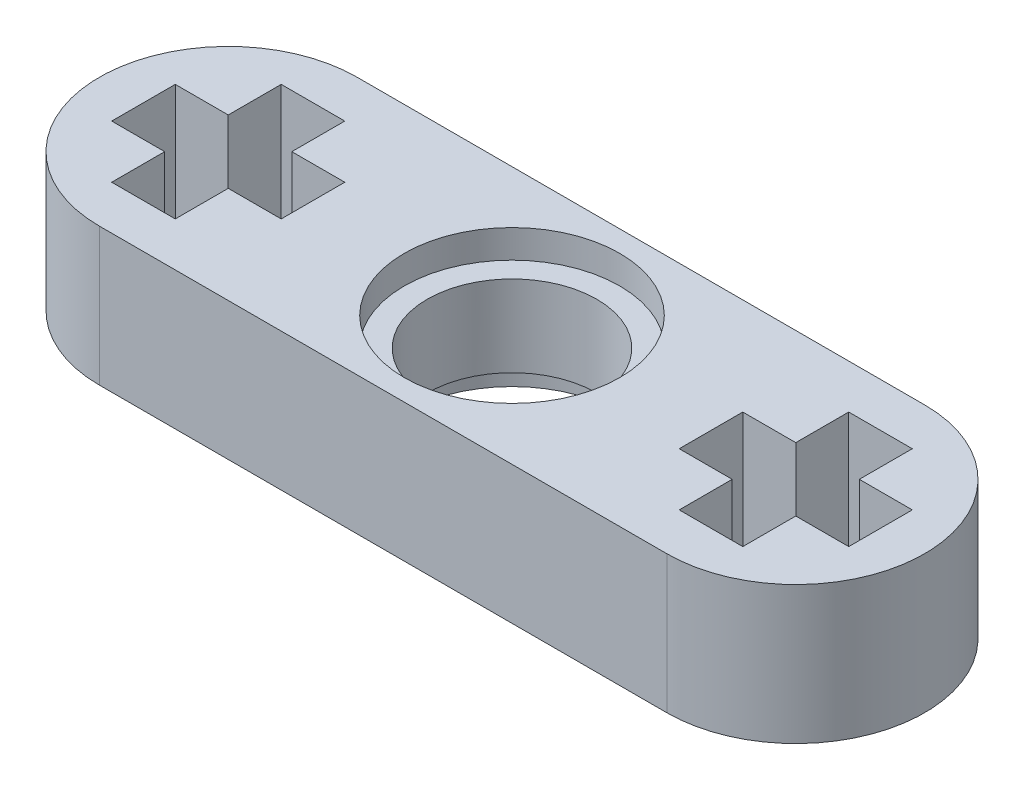
SolidWorks part; units mm, degrees
ref_plane "Front Plane" through (0, 0, 0) normal (0, 0, 1) x (1, 0, 0)
ref_plane "Top Plane" through (0, 0, 0) normal (0, 1, 0) x (1, 0, 0)
ref_plane "Right Plane" through (0, 0, 0) normal (1, 0, 0) x (0, 0, -1)
sketch "Sketch1" plane through (0, 0, 0) normal (0, 1, 0) x (1, 0, 0)
  line L0 (-8.035, 0) -> (-8.0349, 0) construction
  line L1 (-55, 0) -> (55, 0) construction
  line L2 (-8.035, 3.65) -> (8.035, 3.65)
  line L3 (-8.035, -3.65) -> (8.035, -3.65)
  line L4 (-11.685, 0) -> (-11.685, -5.5699) construction
  line L5 (-10.435, 0) -> (-10.435, -5.5699) construction
  line L6 (7.135, 2.4) -> (7.135, 0.9)
  line L7 (7.135, 2.4) -> (8.935, 2.4)
  line L8 (7.135, -2.4) -> (8.935, -2.4)
  line L9 (8.935, 2.4) -> (8.935, 0.9)
  line L10 (7.135, 2.4) -> (8.935, -2.4) construction
  line L11 (7.135, -2.4) -> (8.935, 2.4) construction
  line L12 (10.435, -0.9) -> (8.935, -0.9)
  line L13 (10.435, -0.9) -> (10.435, 0.9)
  line L14 (5.635, -0.9) -> (5.635, 0.9)
  line L15 (10.435, 0.9) -> (8.935, 0.9)
  line L16 (10.435, -0.9) -> (5.635, 0.9) construction
  line L17 (5.635, -0.9) -> (10.435, 0.9) construction
  line L18 (7.135, 0.9) -> (5.635, 0.9)
  line L19 (7.135, -0.9) -> (5.635, -0.9)
  line L20 (7.135, -0.9) -> (7.135, -2.4)
  line L21 (8.935, -0.9) -> (8.935, -2.4)
  line L34 (-8.935, 2.4001) -> (-8.935, 0.9001)
  line L35 (-8.935, 2.4001) -> (-7.135, 2.4001)
  line L36 (-8.935, -2.3999) -> (-7.135, -2.3999)
  line L37 (-7.135, 2.4001) -> (-7.135, 0.9001)
  line L38 (-5.635, -0.8999) -> (-7.135, -0.8999)
  line L39 (-5.635, -0.8999) -> (-5.635, 0.9001)
  line L40 (-10.435, -0.8999) -> (-10.435, 0.9001)
  line L41 (-5.635, 0.9001) -> (-7.135, 0.9001)
  line L42 (-8.935, 0.9001) -> (-10.435, 0.9001)
  line L43 (-8.935, -0.8999) -> (-10.435, -0.8999)
  line L44 (-8.935, -0.8999) -> (-8.935, -2.3999)
  line L45 (-7.135, -0.8999) -> (-7.135, -2.3999)
  line L46 (-8.935, 0.9001) -> (-7.135, -0.8999) construction
  line L47 (-8.035, 0.0001) -> (-7.135, 0.9001) construction
  line L48 (-5.635, 0) -> (8.035, 0) construction
  arc A0 (-8.035, 3.65) -> (-8.035, -3.65) centre (-8.035, 0) ccw
  arc A1 (8.035, -3.65) -> (8.035, 3.65) centre (8.035, 0) ccw
  circle A2 centre (0, 0) radius 2.4
  point P5 (0, 0)
  point P17 (8.035, 0)
  point P18 (8.035, 0)
  point P29 (11.685, 0)
  point P32 (10.435, 0)
  dimension "D3" = 1.25
  dimension "D5" = 1.8
  dimension "D1" = 7.3
  dimension "D2" = 23.37
  dimension "D4" = 1.25
  dimension "D6" = 1.8
  dimension "D7" = 8.035
  dimension "D8" = 8.035
extrude "Boss-Extrude1" add sketch "Sketch1" along normal blind 3.9
sketch "Sketch2" plane through (0, 3.9, 0) normal (0, 1, 0) x (1, 0, 0)
  circle A0 centre (0, 0) radius 3.05
extrude "Cut-Extrude1" cut sketch "Sketch2" against normal blind 0.8
sketch "Sketch3" plane through (0, 0, 0) normal (0, -1, 0) x (-1, 0, 0)
  circle A0 centre (0, 0) radius 3.05
extrude "Cut-Extrude2" cut sketch "Sketch3" against normal blind 0.8
